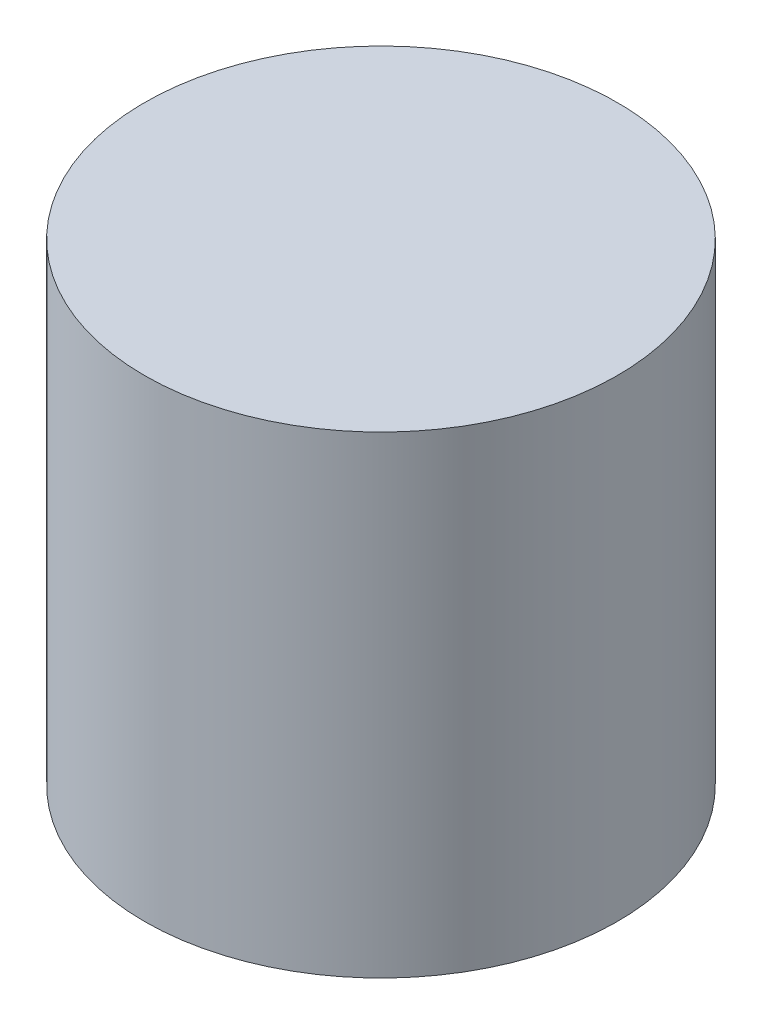
SolidWorks part; units mm, degrees
ref_plane "Front Plane" through (0, 0, 0) normal (0, 0, 1) x (1, 0, 0)
ref_plane "Top Plane" through (0, 0, 0) normal (0, 1, 0) x (1, 0, 0)
ref_plane "Right Plane" through (0, 0, 0) normal (1, 0, 0) x (0, 0, -1)
sketch "Sketch1" plane through (0, 0, 0) normal (0, 1, 0) x (1, 0, 0)
  circle A0 centre (0, 0) radius 1.5
extrude "Boss-Extrude1" add sketch "Sketch1" along normal blind 3
